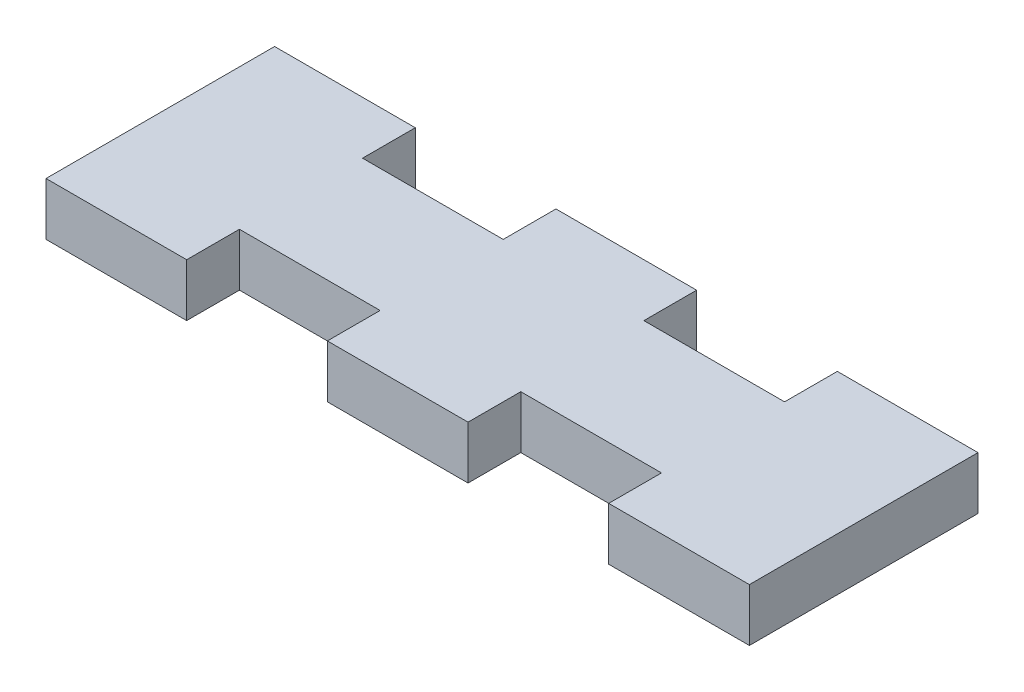
SolidWorks part; units mm, degrees
material "Pino"
ref_plane "Piano frontale" through (0, 0, 0) normal (0, 0, 1) x (1, 0, 0)
ref_plane "Piano superiore" through (0, 0, 0) normal (0, 1, 0) x (1, 0, 0)
ref_plane "Piano destro" through (0, 0, 0) normal (1, 0, 0) x (0, 0, -1)
sketch "Schizzo3" plane through (0, 0, 0) normal (0, 1, 0) x (1, 0, 0)
  line L0 (-20, -3.5) -> (-20, -6.5)
  line L1 (-20, -3.5) -> (20, -3.5) construction
  line L2 (-20, -3.5) -> (-20, 3.5)
  line L3 (-20, 3.5) -> (20, 3.5) construction
  line L4 (20, -3.5) -> (20, 3.5)
  line L5 (-20, -3.5) -> (20, 3.5) construction
  line L6 (-20, 3.5) -> (20, -3.5) construction
  line L7 (-20, -6.5) -> (-12, -6.5)
  line L8 (-12, -6.5) -> (-12, -3.5)
  line L9 (-12, -3.5) -> (-4, -3.5)
  line L10 (-4, -3.5) -> (-4, -6.5)
  line L11 (-4, -6.5) -> (4, -6.5)
  line L12 (4, -6.5) -> (4, -3.5)
  line L13 (20, 6.5) -> (20, 3.5)
  line L14 (4, -3.5) -> (12, -3.5)
  line L15 (12, -6.5) -> (20, -6.5)
  line L16 (12, 3.5) -> (12, 6.5)
  line L17 (12, 6.5) -> (20, 6.5)
  line L18 (12, -3.5) -> (12, -6.5)
  line L19 (4, 3.5) -> (12, 3.5)
  line L20 (20, -6.5) -> (20, -3.5)
  line L21 (-20, 0) -> (20, 0) construction
  line L22 (4, 6.5) -> (4, 3.5)
  line L23 (-4, 6.5) -> (4, 6.5)
  line L24 (-4, 3.5) -> (-4, 6.5)
  line L25 (-12, 3.5) -> (-4, 3.5)
  line L26 (-12, 6.5) -> (-12, 3.5)
  line L27 (-20, 6.5) -> (-12, 6.5)
  line L28 (-20, 3.5) -> (-20, 6.5)
  point P0 (0, 0)
  dimension "D1" = 40
  dimension "D2" = 7
  dimension "D3" = 3
extrude "Estrusione-Estrusione2" add sketch "Schizzo3" along normal mid plane 3
